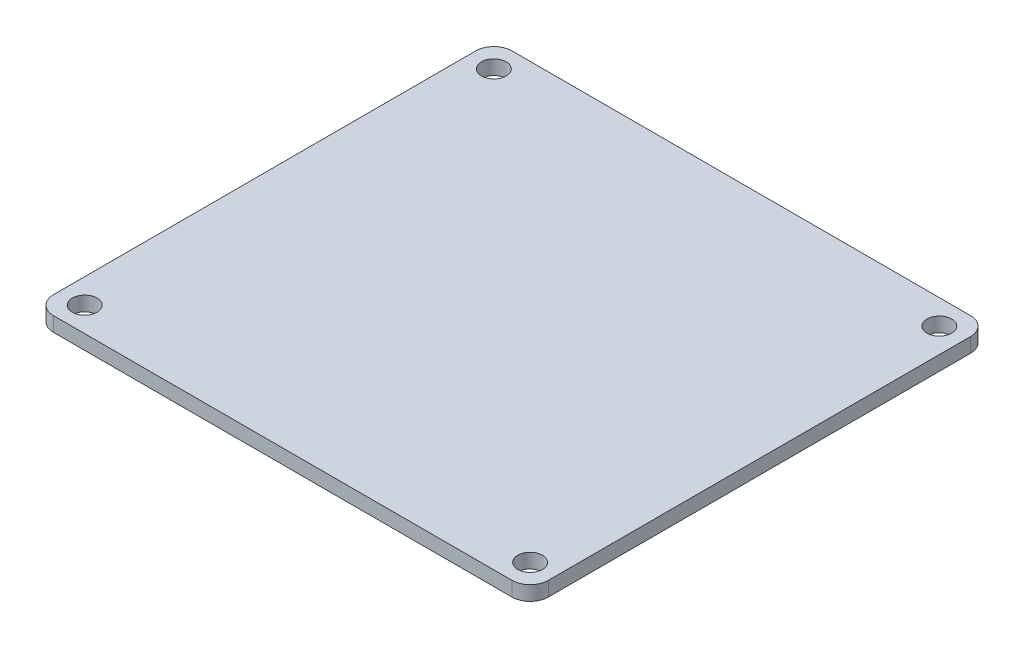
SolidWorks part; units mm, degrees
ref_plane "Front" through (0, 0, 0) normal (0, 0, 1) x (1, 0, 0)
ref_plane "Top" through (0, 0, 0) normal (0, 1, 0) x (1, 0, 0)
ref_plane "Right" through (0, 0, 0) normal (1, 0, 0) x (0, 0, -1)
sketch "ｽｹｯﾁ1" plane through (0, 0, 0) normal (0, 1, 0) x (1, 0, 0)
  line L1 (31.6, 31.6) -> (-31.6, 31.6)
  line L2 (34.1, 29.1) -> (34.1, -29.1)
  line L3 (31.6, -31.6) -> (-31.6, -31.6)
  line L4 (-34.1, 29.1) -> (-34.1, -29.1)
  line L5 (34.1, 31.6) -> (-34.1, -31.6) construction
  line L6 (34.1, -31.6) -> (-34.1, 31.6) construction
  arc A0 (-31.6, -31.6) -> (-34.1, -29.1) centre (-31.6, -29.1) cw
  arc A1 (34.1, -29.1) -> (31.6, -31.6) centre (31.6, -29.1) cw
  arc A2 (31.6, 31.6) -> (34.1, 29.1) centre (31.6, 29.1) cw
  arc A3 (-31.6, 31.6) -> (-34.1, 29.1) centre (-31.6, 29.1) ccw
  circle A4 centre (-30.7, 28.2) radius 1.7
  circle A5 centre (30.7, 28.2) radius 1.7
  circle A6 centre (-30.7, -28.2) radius 1.7
  circle A7 centre (30.7, -28.2) radius 1.7
  point P0 (0, 0)
  point P26 (0, 0)
  point P28 (27, -22.9068)
  dimension "D3" = 2.5
  dimension "D5" = 3.4
  dimension "D1" = 63.2
  dimension "D2" = 68.2
  dimension "D4" = 3.4
  dimension "D6" = 3.4
  dimension "D7" = 3.4
  dimension "D8" = 3.4
extrude "ﾎﾞｽ - 押し出し2" add sketch "ｽｹｯﾁ1" along normal blind 2
